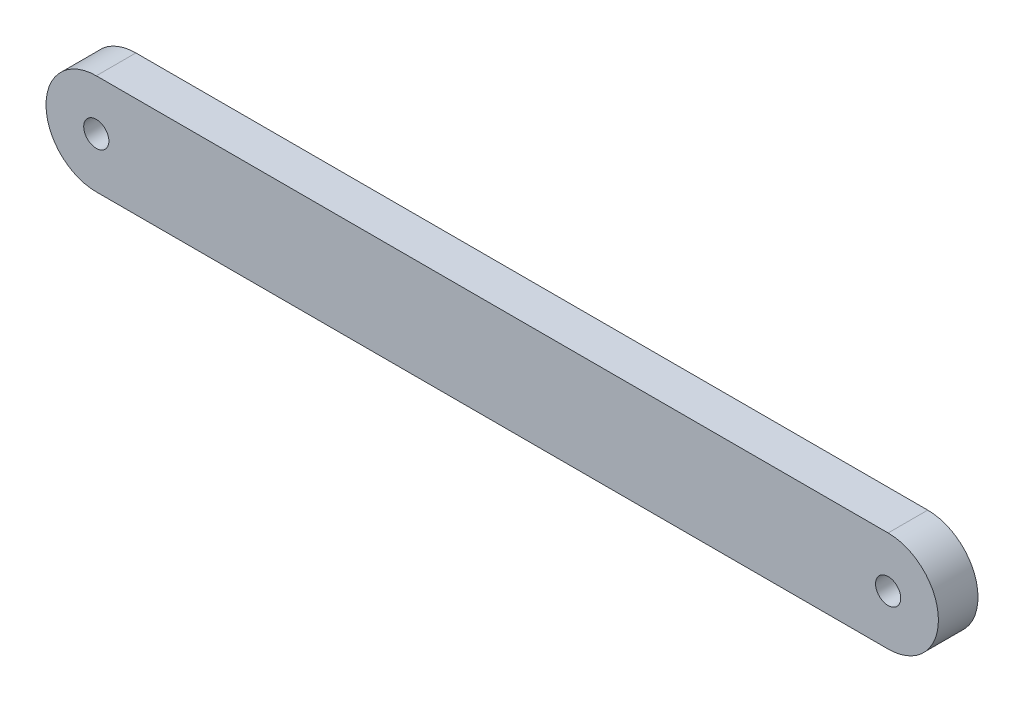
SolidWorks part; units mm, degrees
ref_plane "Front Plane" through (0, 0, 0) normal (0, 0, 1) x (1, 0, 0)
ref_plane "Top Plane" through (0, 0, 0) normal (0, 1, 0) x (1, 0, 0)
ref_plane "Right Plane" through (0, 0, 0) normal (1, 0, 0) x (0, 0, -1)
sketch "Sketch1" plane through (0, 0, 0) normal (0, 0, 1) x (1, 0, 0)
  line L0 (0, 12.7) -> (200, 12.7)
  line L1 (0, -12.7) -> (200, -12.7)
  arc A0 (0, 12.7) -> (0, -12.7) centre (0, 0) ccw
  arc A1 (200, -12.7) -> (200, 12.7) centre (200, 0) ccw
  circle A2 centre (0, 0) radius 3.175
  circle A3 centre (200, 0) radius 3.175
  dimension "D1" = 25.4
  dimension "D3" = 6.35
  dimension "D2" = 200
extrude "Boss-Extrude1" add sketch "Sketch1" along normal blind 10
